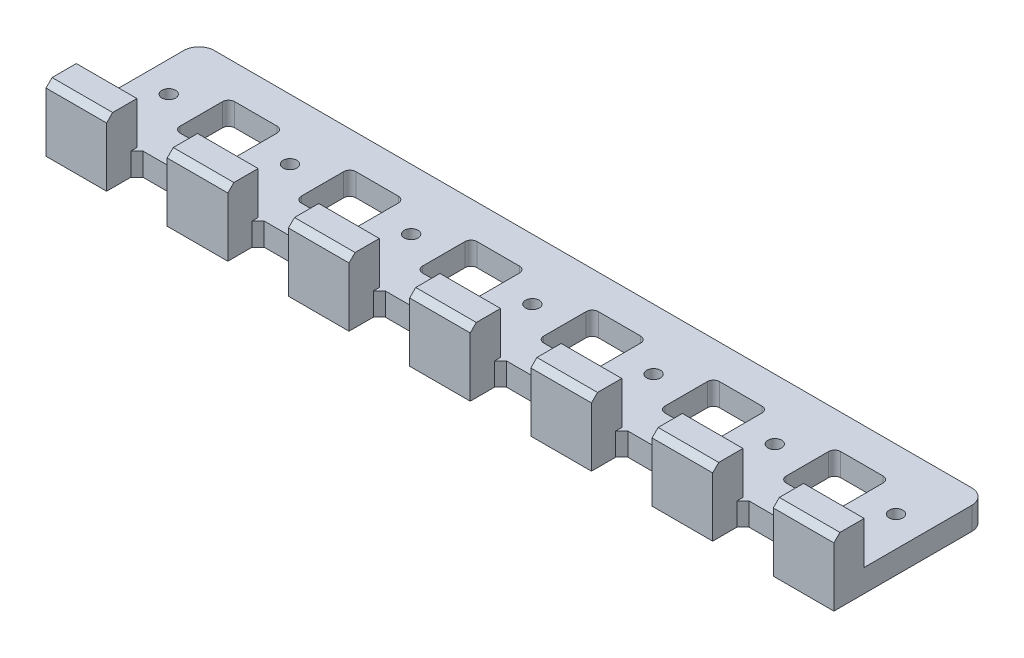
SolidWorks part; units mm, degrees
ref_plane "Front Plane" through (0, 0, 0) normal (0, 0, 1) x (1, 0, 0)
ref_plane "Top Plane" through (0, 0, 0) normal (0, 1, 0) x (1, 0, 0)
ref_plane "Right Plane" through (0, 0, 0) normal (1, 0, 0) x (0, 0, -1)
sketch "Sketch1" plane through (0, 0, 0) normal (0, 1, 0) x (1, 0, 0)
  line L1 (-10, 0) -> (10, 0)
  line L2 (-10, 0) -> (-10, -50.5)
  line L3 (-10, -50.5) -> (10, -50.5)
  line L4 (10, 0) -> (10, -50.5)
  point P4 (0, 0)
  dimension "D1" = 20
  dimension "D2" = 50.5
extrude "Boss-Extrude1" add sketch "Sketch1" along normal blind 7.5
sketch "Sketch2" plane through (0, 7.5, 0) normal (0, 1, 0) x (1, 0, 0)
  line L0 (10, -50.5) -> (10, 0) construction
  line L1 (-10, -50.5) -> (10, -50.5)
  line L2 (-10, -50.5) -> (-10, -40.5)
  line L3 (-10, -40.5) -> (10, -40.5)
  line L4 (10, -50.5) -> (10, -40.5)
  dimension "D1" = 10
extrude "Boss-Extrude2" add sketch "Sketch2" along normal blind 14.01
pattern_linear "LPattern1" count 7 spacing 40 along (1, 0, 0) of bodies 102
sketch "Sketch4" plane through (-10, 0, 0) normal (-1, 0, 0) x (0, 0, 1)
  line L0 (0, 0) -> (50.5, 0) construction
  line L1 (0, 7.5) -> (40.5, 7.5)
  line L2 (0, 7.5) -> (0, 0)
  line L3 (0, 0) -> (40.5, 0)
  line L4 (40.5, 7.5) -> (40.5, 0)
  line L5 (40.5, 21.51) -> (40.5, 7.5) construction
extrude "Boss-Extrude3" add sketch "Sketch4" against normal through all
sketch "Sketch5" plane through (0, 0, 0) normal (0, -1, 0) x (1, 0, 0)
  line L3 (250, 0) -> (-10, 0) construction
  line L4 (240, 50.5) -> (240, 0) construction
  line L5 (230, 50.5) -> (250, 50.5) construction
  line L6 (200, 50.5) -> (200, 0) construction
  line L7 (190, 50.5) -> (210, 50.5) construction
  line L8 (250, 20) -> (-10.0809, 20) construction
  line L9 (250, 0) -> (250, 50.5) construction
  line L11 (250, 0) -> (-10, 0) construction
  point P16 (240, 20)
  dimension "D1" = 20
hole_wizard "M4 Clearance Hole1" positions "Sketch5" profile "Sketch6" hole size "M4" standard "ANSI Metric" end condition up to next
sketch "Sketch6" plane through (240, 0, 20) normal (1, 0, 0) x (0, 0, -1)
  line L0 (0, 0) -> (0, 7.5)
  line L1 (0, 7.5) -> (2.25, 7.5)
  line L2 (2.25, 7.5) -> (2.25, 0)
  line L5 (2.25, 0) -> (0, 0)
  line L11 (0, -6.35) -> (0, 107.95) construction
  dimension "Thru Hole Dia." = 4.5
  dimension "Thru Hole Depth" = 7.5
pattern_linear "LPattern2" count 7 spacing 40 along (-1, 0, 0) of "M4 Clearance Hole1"
sketch "Sketch7" plane through (0, 7.5, 0) normal (0, 1, 0) x (1, 0, 0)
  line L0 (250, -20.25) -> (-10, -20.25) construction
  line L1 (229, -29.25) -> (211, -29.25)
  line L2 (229, -29.25) -> (229, -11.25)
  line L3 (229, -11.25) -> (211, -11.25)
  line L4 (211, -29.25) -> (211, -11.25)
  line L5 (250, -40.5) -> (250, 0) construction
  line L6 (-10, 0) -> (-10, -40.5) construction
  line L7 (220, -40.5) -> (220, 0) construction
  line L8 (230, -40.5) -> (210, -40.5) construction
  line L9 (250, 0) -> (-10, 0) construction
  point P10 (229, -20.25)
  point P17 (220, -29.25)
  dimension "D1" = 18
  dimension "D2" = 18
extrude "Cut-Extrude1" cut sketch "Sketch7" against normal through all
fillet "Fillet1" radius 2 4 edges at (211, 3.75, 11.25) (229, 3.75, 11.25) (229, 3.75, 29.25) (211, 3.75, 29.25)
pattern_linear "LPattern3" count 6 spacing 40 along (-1, 0, 0) of "Fillet1", "Cut-Extrude1"
fillet "Fillet2" radius 5 2 edges at (-10, 3.75, 0) (250, 3.75, 0)
chamfer "Chamfer1" distance 2 angle 45 7 edges at (240, 21.51, 50.5) (200, 21.51, 50.5) (160, 21.51, 50.5) (120, 21.51, 50.5) (80, 21.51, 50.5) (40, 21.51, 50.5) (0, 21.51, 50.5)
chamfer "Chamfer2" distance 2 angle 45 12 edges at (230, 3.75, 40.5) (210, 3.75, 40.5) (190, 3.75, 40.5) (170, 3.75, 40.5) (150, 3.75, 40.5) (110, 3.75, 40.5) (130, 3.75, 40.5) (90, 3.75, 40.5) (70, 3.75, 40.5) (30, 3.75, 40.5) (50, 3.75, 40.5) (10, 3.75, 40.5)
equation "\"D2@Sketch7\"=\"D1@Sketch7\""
